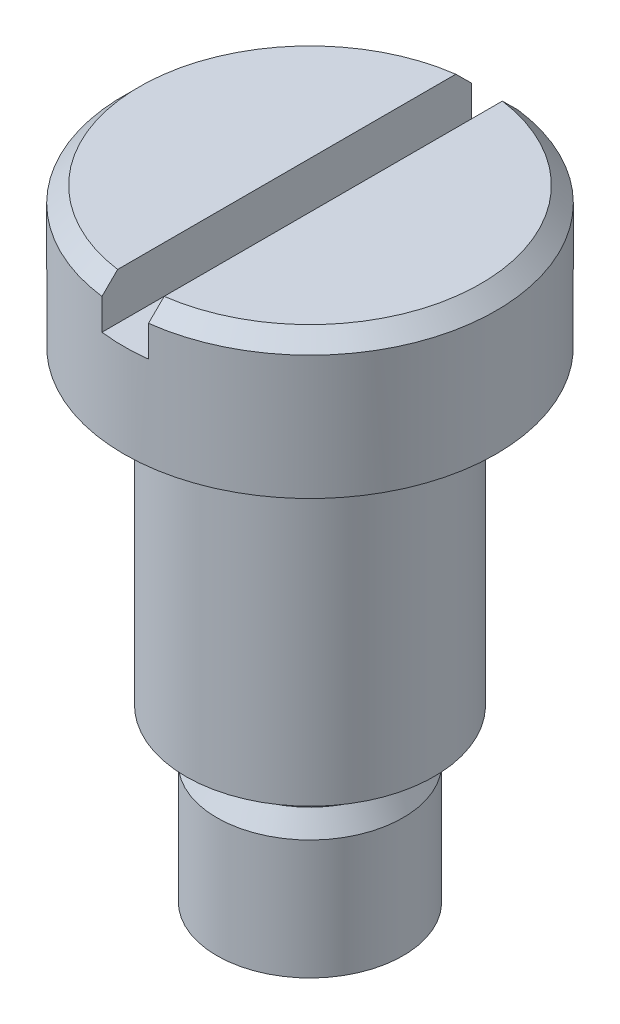
SolidWorks part; units mm, degrees
ref_plane "Front Plane" through (0, 0, 0) normal (0, 0, 1) x (1, 0, 0)
ref_plane "Top Plane" through (0, 0, 0) normal (0, 1, 0) x (1, 0, 0)
ref_plane "Right Plane" through (0, 0, 0) normal (1, 0, 0) x (0, 0, -1)
sketch "Sketch1" plane through (0, 0, 0) normal (0, 0, 1) x (1, 0, 0)
  line L0 (0, 0) -> (0, 40) construction
  line L1 (0, 40) -> (12, 40)
  line L2 (12, 40) -> (12, 31)
  line L3 (12, 31) -> (8, 31)
  line L4 (8, 31) -> (8, 11)
  line L5 (8, 11) -> (5.25, 11)
  line L6 (5.25, 11) -> (5.25, 9)
  line L7 (6, 0) -> (0, 0)
  line L9 (6, 7.701) -> (6, 0)
  line L10 (0, 0) -> (0, 40)
  line L11 (5.25, 9) -> (6, 7.701)
  dimension "D1" = 40
  dimension "D2" = 5.25
  dimension "D3" = 31
  dimension "D4" = 9
  dimension "D5" = 11
  dimension "D6" = 16
  dimension "D7" = 6
  dimension "D8" = 24
  dimension "D9" = 30
revolve "Revolve1" add sketch "Sketch1" angle 360 about L0
cosmetic thread "Cosmetic Thread1" parameters "D1"=5, "D2"=10.072
sketch "Sketch2" plane through (0, 0, 0) normal (0, 0, 1) x (1, 0, 0)
  line L0 (12, 40) -> (-12, 40) construction
  line L1 (-1.5, 40) -> (1.5, 40)
  line L2 (-1.5, 40) -> (-1.5, 37)
  line L3 (-1.5, 37) -> (1.5, 37)
  line L4 (1.5, 40) -> (1.5, 37)
  line L5 (0, 0) -> (0, 31) construction
  line L6 (-8, 31) -> (8, 31) construction
  dimension "D1" = 3
  dimension "D2" = 3
extrude "Cut-Extrude1" cut sketch "Sketch2" against normal through all both and the other way through all
chamfer "Chamfer1" distance 1 angle 45 2 edges at (12, 40, 0) (-12, 40, 0)
